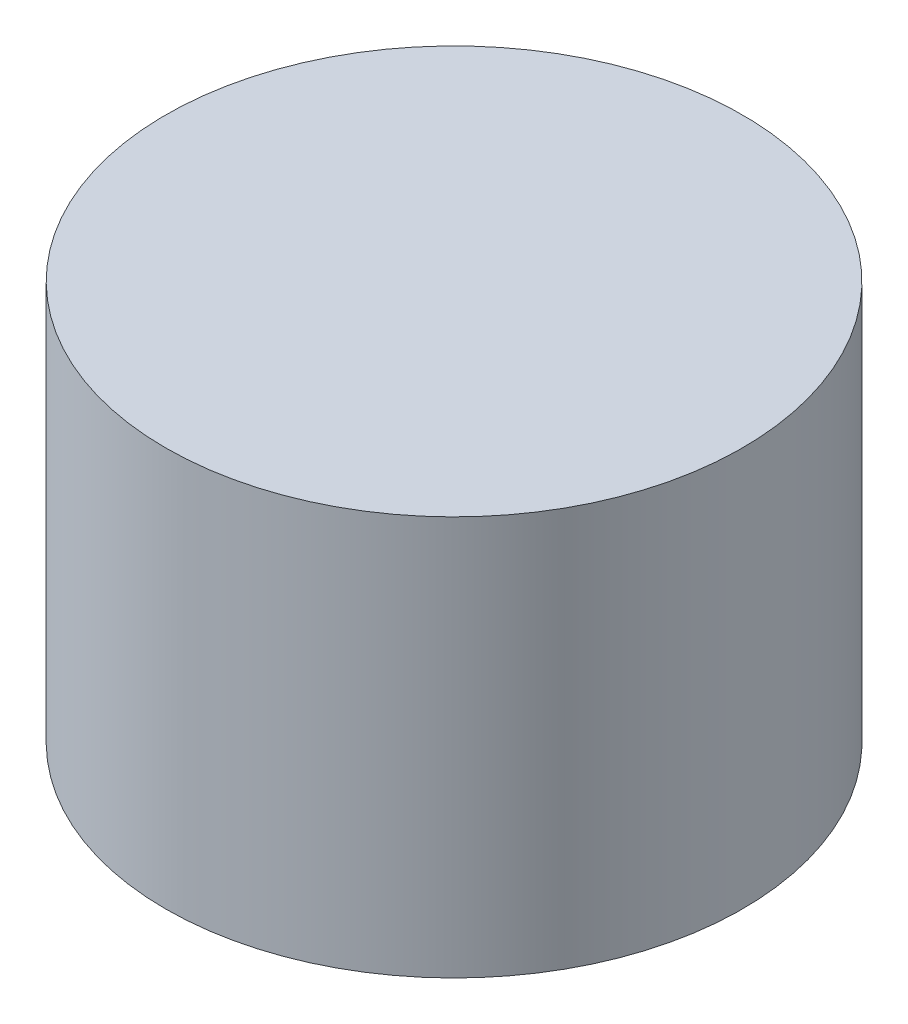
SolidWorks part; units mm, degrees
material "Glass"
ref_plane "Front Plane" through (0, 0, 0) normal (0, 0, 1) x (1, 0, 0)
ref_plane "Top Plane" through (0, 0, 0) normal (0, 1, 0) x (1, 0, 0)
ref_plane "Right Plane" through (0, 0, 0) normal (1, 0, 0) x (0, 0, -1)
sketch "Sketch1" plane through (0, 0, 0) normal (0, 1, 0) x (1, 0, 0)
  circle A0 centre (0, 0) radius 13
  dimension "D1" = 26
extrude "Boss-Extrude1" add sketch "Sketch1" along normal blind 18
